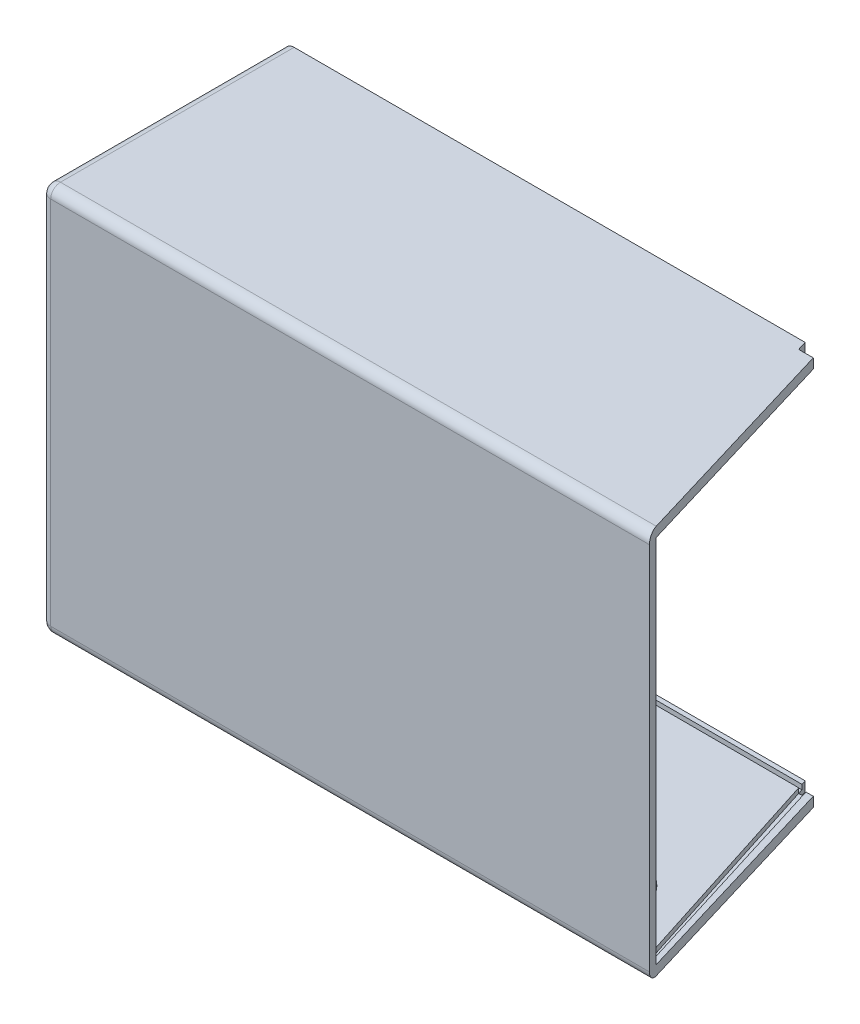
SolidWorks part; units mm, degrees
ref_plane "Front Plane" through (0, 0, 0) normal (0, 0, 1) x (1, 0, 0)
ref_plane "Top Plane" through (0, 0, 0) normal (0, 1, 0) x (1, 0, 0)
ref_plane "Right Plane" through (0, 0, 0) normal (1, 0, 0) x (0, 0, -1)
sketch "Sketch2" plane through (0, 0, 0) normal (0, 1, 0) x (1, 0, 0)
  line L1 (-108.6456, -36.8346) -> (-108.6456, 13.1654)
  line L2 (-108.6456, 13.1654) -> (1.3544, 13.1654)
  line L3 (1.3544, 13.1654) -> (16.3544, -36.8346)
  line L5 (16.3544, -36.8346) -> (-108.6456, -36.8346)
  dimension "D1" = 125
  dimension "D2" = 50
  dimension "D3" = 110
extrude "Boss-Extrude1" add sketch "Sketch2" along normal blind 80
shell "Shell1" thickness 2
sketch "Sketch6" plane through (0, 0, 0) normal (0, -1, 0) x (-1, 0, 0)
  line L0 (-1.3544, 13.1654) -> (-1.9291, 11.2497)
  line L1 (-16.3544, -36.8346) -> (-1.3544, 13.1654) construction
  line L2 (-1.9291, 11.2497) -> (1.0709, 11.2497)
  line L3 (1.0709, 11.2497) -> (1.6456, 13.1654)
  line L4 (-1.3544, 13.1654) -> (108.6456, 13.1654) construction
  line L5 (-1.3544, 13.1654) -> (1.6456, 13.1654)
  dimension "D1" = 2
  dimension "D2" = 2
  dimension "D3" = 3
extrude "Cut-Extrude2" cut sketch "Sketch6" against normal blind 92
sketch "Sketch7" plane through (0, 2, 0) normal (0, 1, 0) x (1, 0, 0)
  line L0 (-1.0709, 11.2497) -> (-106.6456, 11.3864)
  line L1 (-106.6456, 13.1654) -> (-106.6456, -34.8346) construction
  line L2 (-106.6456, 11.3864) -> (-106.6456, 12.2075)
  line L3 (-106.6456, 12.2075) -> (-1.3582, 12.2075)
  line L4 (-1.0709, 11.2497) -> (-1.6456, 13.1654) construction
  line L5 (-1.3582, 12.2075) -> (-1.0709, 11.2497)
  line L6 (-1.6456, 13.1654) -> (-106.6456, 13.1654) construction
  dimension "D1" = 1
extrude "Cut-Extrude3" cut sketch "Sketch7" against normal blind 1
sketch "Sketch9" plane through (0, 78, 0) normal (0, -1, 0) x (-1, 0, 0)
  line L0 (1.0709, 11.2497) -> (106.6456, 11.209)
  line L1 (106.6456, 13.1654) -> (106.6456, -34.8346) construction
  line L2 (106.6456, 12.5932) -> (1.3582, 12.2075)
  line L3 (1.0709, 11.2497) -> (1.6456, 13.1654) construction
  line L4 (1.3582, 12.2075) -> (1.0709, 11.2497)
  arc A0 (106.6456, 11.209) -> (106.6456, 12.5932) centre (-1687.5043, 11.9011) ccw
  dimension "D1" = 1
extrude "Cut-Extrude4" cut sketch "Sketch9" against normal blind 1
sketch "Sketch11" plane through (4.8661, 0, -1.4598) normal (0.9578, 0, -0.2873) x (-0.2873, 0, -0.9578)
  line L0 (10.2209, 80) -> (10.2209, 0) construction
  line L1 (10.2209, 78) -> (-37.9806, 78)
  line L2 (10.2209, 78) -> (10.2209, 2)
  line L3 (10.2209, 2) -> (-37.9806, 2)
  line L4 (-37.9806, 78) -> (-37.9806, 2)
  line L5 (-39.9806, 80) -> (10.2209, 80) construction
  line L6 (-39.9806, 0) -> (10.2209, 0) construction
  line L7 (-39.9806, 80) -> (-39.9806, 0) construction
  dimension "D1" = 2
  dimension "D2" = 2
  dimension "D3" = 2
extrude "Cut-Extrude6" cut sketch "Sketch11" against normal blind 2
sketch "Sketch12" plane through (0, 0, -11.2497) normal (0, 0, -1) x (-1, 0, 0)
  line L0 (0.1589, 78) -> (-1.9291, 78)
  line L1 (-1.9291, 78) -> (-1.9291, 2)
  line L2 (-1.9291, 2) -> (0.1589, 2)
  line L3 (0.1589, 2) -> (0.1589, 78)
extrude "Cut-Extrude7" cut sketch "Sketch12" against normal blind 2
sketch "Sketch14" plane through (0, 2, 0) normal (0, 1, 0) x (1, 0, 0)
  line L0 (-1.0709, 11.2497) -> (0.4291, 11.2497)
  line L1 (1.9291, 11.2497) -> (-1.0709, 11.2497) construction
  line L2 (0.4291, 11.2497) -> (14.8219, -35.2063)
  line L3 (13.8641, -35.4937) -> (15.7797, -34.919) construction
  line L4 (14.8219, -35.2063) -> (13.8641, -35.4937)
  line L5 (13.8641, -35.4937) -> (13.6664, -34.8346) construction
  line L6 (13.8641, -35.4937) -> (-1.0709, 11.2497)
extrude "Cut-Extrude9" cut sketch "Sketch14" against normal blind 1
sketch "Sketch15" plane through (0, 78, 0) normal (0, -1, 0) x (-1, 0, 0)
  line L0 (-13.8641, -35.4937) -> (1.0709, 11.2497)
  line L1 (1.0709, 11.2497) -> (-0.4291, 11.2497)
  line L2 (-1.9291, 11.2497) -> (1.0709, 11.2497) construction
  line L3 (-0.4291, 11.2497) -> (-14.8219, -35.2063)
  line L4 (-13.8641, -35.4937) -> (-15.7797, -34.919) construction
  line L5 (-14.8219, -35.2063) -> (-13.8641, -35.4937)
extrude "Cut-Extrude10" cut sketch "Sketch15" against normal blind 1
sketch "Sketch16" plane through (-108.6456, 0, 0) normal (-1, 0, 0) x (0, 0, 1)
  line L0 (36.8346, 80) -> (36.8346, 0) construction
  line L1 (-13.1654, 0) -> (36.8346, 0) construction
  circle A0 centre (26.8346, 10) radius 3.5
  dimension "D1" = 7
  dimension "D2" = 10
  dimension "D3" = 10
extrude "Cut-Extrude11" cut sketch "Sketch16" against normal blind 2
sketch "Sketch17" plane through (0, 0, 34.8346) normal (0, 0, -1) x (-1, 0, 0)
  circle A0 centre (89.1359, 72.0863) radius 4
  circle A1 centre (-3.8641, 72.0863) radius 4
  circle A2 centre (-3.8641, 8.0863) radius 4
  circle A3 centre (89.1359, 8.0863) radius 4
  circle A4 centre (-3.8641, 72.0863) radius 1.5
  circle A5 centre (-3.8641, 8.0863) radius 1.5
  circle A6 centre (89.1359, 72.0863) radius 1.5
  circle A7 centre (89.1359, 8.0863) radius 1.5
  dimension "D1" = 3
  dimension "D2" = 3
  dimension "D3" = 3
  dimension "D4" = 3
  dimension "D5" = 8
  dimension "D6" = 8
  dimension "D7" = 8
  dimension "D8" = 8
  dimension "D9" = 93
  dimension "D10" = 64
  dimension "D11" = 93
  dimension "D12" = 64
extrude "Boss-Extrude2" add sketch "Sketch17" along normal blind 8
fillet "Fillet1" radius 2 8 edges at (-108.6456, 40, 36.8346) (-46.1456, 0, 36.8346) (-108.6456, 0, 11.8346) (-108.6456, 80, 11.8346) (-46.1456, 80, 36.8346) (-46.496, 2, 34.8346) (-106.6456, 40, 34.8346) (-106.6456, 2, 11.7241)
